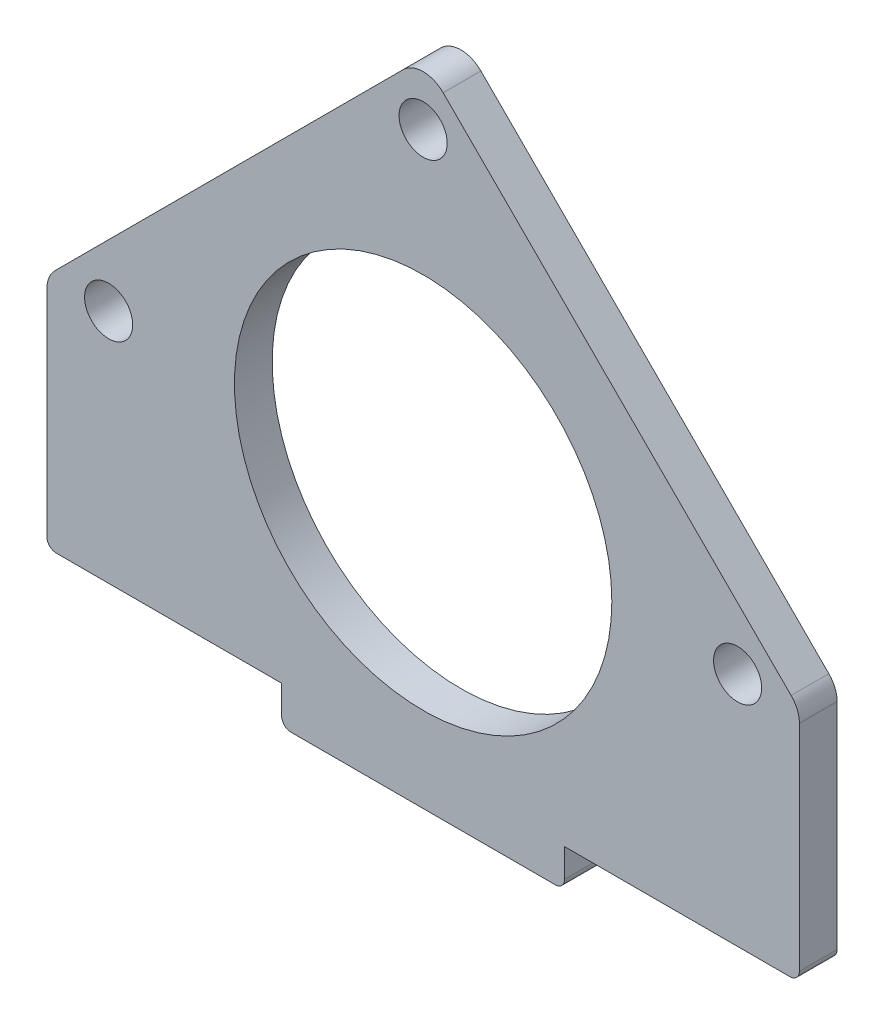
SolidWorks part; units mm, degrees
ref_plane "Спереди" through (0, 0, 0) normal (0, 0, 1) x (1, 0, 0)
ref_plane "Сверху" through (0, 0, 0) normal (0, 1, 0) x (1, 0, 0)
ref_plane "Справа" through (0, 0, 0) normal (1, 0, 0) x (0, 0, -1)
sketch "Эскиз1" plane through (0, 0, 0) normal (0, 0, 1) x (1, 0, 0)
  line L0 (-39.8808, 0) -> (0, 39.8808)
  line L1 (-39.8808, 0) -> (-39.8808, -25)
  line L2 (-39.8808, -25) -> (-15, -25)
  line L3 (-15, -25) -> (-15, -29)
  line L4 (15, -29) -> (-15, -29)
  line L5 (15, -29) -> (15, -25)
  line L6 (15, -25) -> (39.8808, -25)
  line L11 (39.8808, -25) -> (39.8808, 0)
  line L12 (0, 39.8808) -> (39.8808, 0)
  circle A0 centre (0, 0) radius 20
  circle A1 centre (-33.333, 0) radius 2.55
  circle A2 centre (0, 33.333) radius 2.55
  circle A3 centre (33.333, 0) radius 2.55
  point P4 (0, 0)
  point P23 (0, 0)
  point P27 (0, 0)
  dimension "D2" = 40
  dimension "D4" = 5.1
  dimension "D6" = 56.4
  dimension "D5" = 47.14
  dimension "D7" = 90
  dimension "D8" = 4
  dimension "D9" = 25
  dimension "D1" = 30
  dimension "D3" = 3
extrude "Бобышка-Вытянуть2" add sketch "Эскиз1" along normal blind 4
fillet "Скругление1" radius 3 3 edges at (39.8808, 0, 2) (-39.8808, 0, 2) (0, 39.8808, 2)
fillet "Скругление2" radius 1 4 edges at (15, -29, 2) (39.8808, -25, 2) (-15, -29, 2) (-39.8808, -25, 2)
